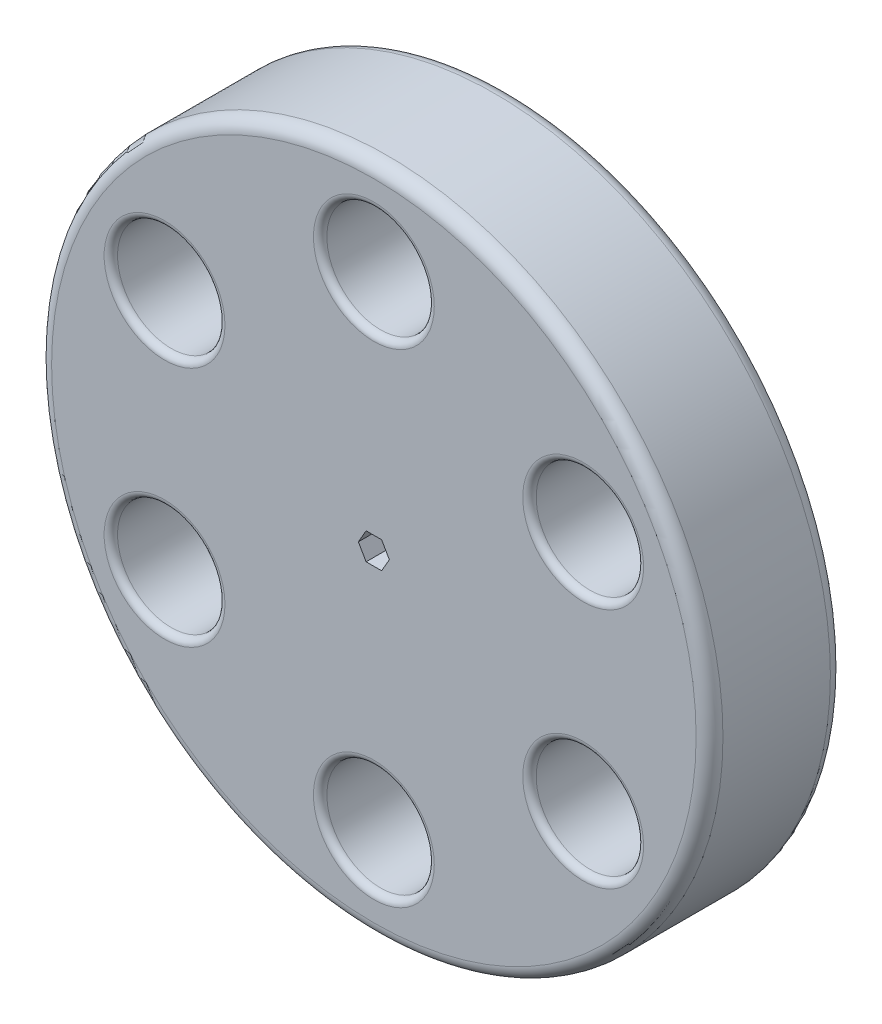
SolidWorks part; units mm, degrees
material "ABS"
ref_plane "Front" through (0, 0, 0) normal (0, 0, 1) x (1, 0, 0)
ref_plane "Top" through (0, 0, 0) normal (0, 1, 0) x (1, 0, 0)
ref_plane "Right" through (0, 0, 0) normal (1, 0, 0) x (0, 0, -1)
sketch "Sketch1" plane through (0, 0, 0) normal (0, 0, 1) x (1, 0, 0)
  circle A0 centre (0, 0) radius 25
  dimension "D1" = 50
extrude "Boss-Extrude1" add sketch "Sketch1" along normal blind 10
sketch "Sketch2" plane through (0, 0, 10) normal (0, 0, 1) x (1, 0, 0)
  line L1 (1.1547, 0) -> (0.5774, 1)
  line L2 (0.5774, 1) -> (-0.5774, 1)
  line L3 (-0.5774, 1) -> (-1.1547, 0)
  line L4 (-1.1547, 0) -> (-0.5774, -1)
  line L5 (-0.5774, -1) -> (0.5774, -1)
  line L6 (0.5774, -1) -> (1.1547, 0)
  circle A1 centre (0, 0) radius 1 construction
  dimension "D1" = 2
sketch "Sketch3" plane through (0, 0, 10) normal (0, 0, 1) x (1, 0, 0)
  circle A0 centre (0, 18) radius 4
  dimension "D1" = 8
  dimension "D2" = 18
extrude "Cut-Extrude3" cut sketch "Sketch3" against normal through all
pattern_circular "CirPattern1" count 6 over 360 about axis through (0, 0, 0) along (0, 0, 1) of "Cut-Extrude3"
fillet "Fillet1" radius 1 2 edges at (25, 0, 0) (25, 0, 10)
fillet "Fillet2" radius 0.5 12 edges at (-17.5885, -5.5359, 10) (-17.5885, -5.5359, 0) (-4, -18, 0) (-4, -18, 10) (13.5885, -12.4641, 10) (13.5885, -12.4641, 0) (17.5885, 5.5359, 0) (17.5885, 5.5359, 10) (4, 18, 10) (4, 18, 0) (-13.5885, 12.4641, 0) (-13.5885, 12.4641, 10)
extrude "Cut-Extrude4" cut sketch "Sketch2" against normal up to surface (10 mm away) up to face at (-11.0885, -9, 0)
